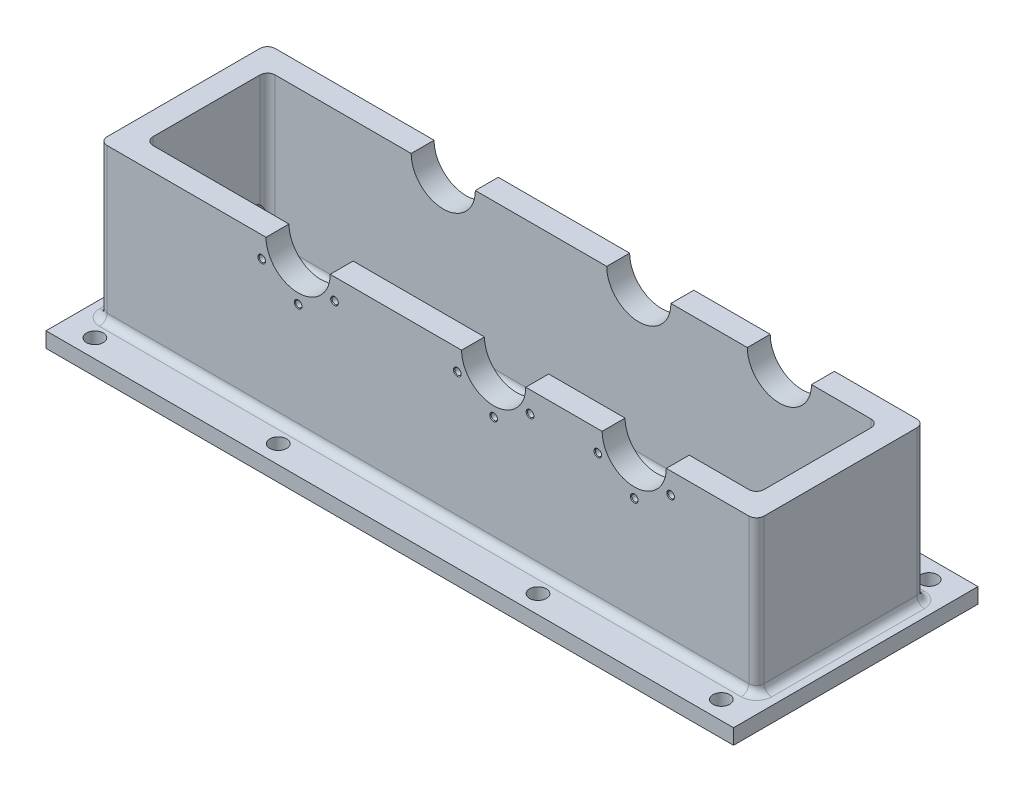
SolidWorks part; units mm, degrees
ref_plane "Front Plane" through (0, 0, 0) normal (0, 0, 1) x (1, 0, 0)
ref_plane "Top Plane" through (0, 0, 0) normal (0, 1, 0) x (1, 0, 0)
ref_plane "Right Plane" through (0, 0, 0) normal (1, 0, 0) x (0, 0, -1)
sketch "Sketch1" plane through (0, 0, 0) normal (0, 1, 0) x (1, 0, 0)
  line L1 (-225, -80) -> (225, -80)
  line L2 (-225, -80) -> (-225, 80)
  line L3 (-225, 80) -> (225, 80)
  line L4 (225, -80) -> (225, 80)
  line L5 (-225, -80) -> (225, 80) construction
  line L6 (-225, 80) -> (225, -80) construction
  point P0 (0, 0)
  dimension "D1" = 160
  dimension "D2" = 450
extrude "Boss-Extrude1" add sketch "Sketch1" along normal blind 10
sketch "Sketch2" plane through (0, 10, 0) normal (0, 1, 0) x (1, 0, 0)
  line L1 (-215, -55) -> (215, -55)
  line L2 (-215, -55) -> (-215, 55)
  line L3 (-215, 55) -> (215, 55)
  line L4 (215, -55) -> (215, 55)
  line L5 (-215, -55) -> (215, 55) construction
  line L6 (-215, 55) -> (215, -55) construction
  line L7 (-200, -40) -> (200, -40)
  line L8 (-200, -40) -> (-200, 40)
  line L9 (-200, 40) -> (200, 40)
  line L10 (200, -40) -> (200, 40)
  line L11 (-200, -40) -> (200, 40) construction
  line L12 (-200, 40) -> (200, -40) construction
  point P0 (0, 0)
  point P6 (0, 0)
  dimension "D1" = 430
  dimension "D2" = 110
  dimension "D3" = 15
  dimension "D4" = 15
extrude "Boss-Extrude2" add sketch "Sketch2" along normal blind 100
sketch "Sketch3" plane through (0, 10, 0) normal (0, 1, 0) x (1, 0, 0)
  line L0 (-225, 80) -> (-225, -80) construction
  line L1 (-60.5, 0) -> (60.5, 0) construction
  line L2 (0, -60.5) -> (0, 60.5) construction
  circle A1 centre (-205, 68) radius 5.5
  circle A2 centre (-85, 68) radius 5.5
  circle A3 centre (-205, -68) radius 5.5
  circle A4 centre (-85, -68) radius 5.5
  circle A5 centre (205, 68) radius 5.5
  circle A6 centre (85, 68) radius 5.5
  circle A7 centre (85, -68) radius 5.5
  circle A8 centre (205, -68) radius 5.5
  dimension "D1" = 11
  dimension "D2" = 20
  dimension "D3" = 120
  dimension "D4" = 68
  dimension "D5" = 68
  dimension "D6" = 120
extrude "Cut-Extrude1" cut sketch "Sketch3" against normal blind 100
sketch "Sketch4" plane through (0, 0, 55) normal (0, 0, 1) x (1, 0, 0)
  line L0 (-215, 110) -> (215, 110) construction
  line L1 (215, 110) -> (215, 10) construction
  circle A0 centre (-85, 110) radius 21
  circle A1 centre (43, 110) radius 21
  circle A2 centre (135, 110) radius 21
  dimension "D1" = 42
  dimension "D2" = 128
  dimension "D3" = 92
  dimension "D4" = 80
extrude "Cut-Extrude2" cut sketch "Sketch4" against normal through all
sketch "Sketch5" plane through (0, 0, 55) normal (0, 0, 1) x (1, 0, 0)
  line L0 (-85, 110) -> (-61.1843, 96.25)
  line L1 (43, 110) -> (66.8157, 96.25)
  line L2 (135, 110) -> (158.8157, 96.25)
  line L3 (-64, 110) -> (22, 110) construction
  line L4 (64, 110) -> (114, 110) construction
  line L5 (156, 110) -> (215, 110) construction
  circle A0 centre (-85, 110) radius 27.5 construction
  circle A1 centre (43, 110) radius 27.5 construction
  circle A2 centre (135, 110) radius 27.5 construction
  dimension "D1" = 55
  dimension "D2" = 30
  dimension "D3" = 30
  dimension "D4" = 30
hole_wizard "M5 Tapped Hole1" positions "3DSketch4" profile "Sketch10" tap size "M5" standard "ISO"
sketch3d "3DSketch4"
  point P0 (158.8157, 96.25, 55)
sketch "Sketch10" plane through (158.8157, 96.25, 55) normal (1, 0, 0) x (0, -1, 0)
  line L0 (0, 0) -> (0, 13.6618)
  line L1 (0, 13.6618) -> (2.1, 12.4)
  line L2 (2.1, 12.4) -> (2.1, 0.425)
  line L3 (2.1, 0.425) -> (2.525, 0)
  line L5 (2.525, 0) -> (0, 0)
  line L6 (-2.1, 0.425) -> (-2.525, 0) construction
  line L10 (0, 13.6618) -> (-2.1, 12.4) construction
  line L11 (0, -6.35) -> (0, 107.95) construction
  dimension "Tap Drill Dia." = 4.2
  dimension "Tap Drill Depth" = 12.4
  dimension "Near C'Sink Dia." = 5.05
  dimension "Near C'Sink Angle" = 90
  dimension "Drill Angle" = 118
hole_wizard "M5 Tapped Hole2" positions "3DSketch5" profile "Sketch11" tap size "M5" standard "ISO"
sketch3d "3DSketch5"
  point P0 (66.8157, 96.25, 55)
sketch "Sketch11" plane through (66.8157, 96.25, 55) normal (1, 0, 0) x (0, -1, 0)
  line L0 (0, 0) -> (0, 13.6618)
  line L1 (0, 13.6618) -> (2.1, 12.4)
  line L2 (2.1, 12.4) -> (2.1, 0.425)
  line L3 (2.1, 0.425) -> (2.525, 0)
  line L5 (2.525, 0) -> (0, 0)
  line L6 (-2.1, 0.425) -> (-2.525, 0) construction
  line L10 (0, 13.6618) -> (-2.1, 12.4) construction
  line L11 (0, -6.35) -> (0, 107.95) construction
  dimension "Tap Drill Dia." = 4.2
  dimension "Tap Drill Depth" = 12.4
  dimension "Near C'Sink Dia." = 5.05
  dimension "Near C'Sink Angle" = 90
  dimension "Drill Angle" = 118
hole_wizard "M5 Tapped Hole3" positions "3DSketch6" profile "Sketch12" tap size "M5" standard "ISO"
sketch3d "3DSketch6"
  point P0 (-61.1843, 96.25, 55)
sketch "Sketch12" plane through (-61.1843, 96.25, 55) normal (1, 0, 0) x (0, -1, 0)
  line L0 (0, 0) -> (0, 13.6618)
  line L1 (0, 13.6618) -> (2.1, 12.4)
  line L2 (2.1, 12.4) -> (2.1, 0.425)
  line L3 (2.1, 0.425) -> (2.525, 0)
  line L5 (2.525, 0) -> (0, 0)
  line L6 (-2.1, 0.425) -> (-2.525, 0) construction
  line L10 (0, 13.6618) -> (-2.1, 12.4) construction
  line L11 (0, -6.35) -> (0, 107.95) construction
  dimension "Tap Drill Dia." = 4.2
  dimension "Tap Drill Depth" = 12.4
  dimension "Near C'Sink Dia." = 5.05
  dimension "Near C'Sink Angle" = 90
  dimension "Drill Angle" = 118
pattern_circular "CirPattern1" count 6 over 360 about axis through (135, 110, -80) along (0, 0, 1) skipping 1, 2, 3 of "M5 Tapped Hole1"
pattern_circular "CirPattern2" count 6 over 360 about axis through (43, 110, -80) along (0, 0, 1) skipping 1, 2, 3 of "M5 Tapped Hole2"
pattern_circular "CirPattern3" count 6 over 360 about axis through (-85, 110, -80) along (0, 0, 1) skipping 1, 2, 3 of "M5 Tapped Hole3"
mirror "Mirror3" about plane through (0, 0, 0) normal (0, 0, 1) of "M5 Tapped Hole1", "M5 Tapped Hole2", "M5 Tapped Hole3", "CirPattern1", "CirPattern2", "CirPattern3"
fillet "Fillet1" radius 5 16 edges at (215, 10, 0) (0, 10, -55) (-215, 10, 0) (0, 10, 55) (-215, 60, 55) (-215, 60, -55) (215, 60, 55) (215, 60, -55) (200, 60, -40) (-200, 60, -40) (-200, 60, 40) (200, 60, 40) (200, 10, 0) (-200, 10, 0) (0, 10, -40) (0, 10, 40)
sketch "Sketch13" plane through (-215, 0, 0) normal (-1, 0, 0) x (0, 0, 1)
  line L0 (50, 10) -> (-50, 10) construction
  circle A0 centre (-30, 30) radius 8
  dimension "D1" = 16
  dimension "D2" = 30
  dimension "D3" = 20
extrude "Cut-Extrude3" cut sketch "Sketch13" against normal blind 100
